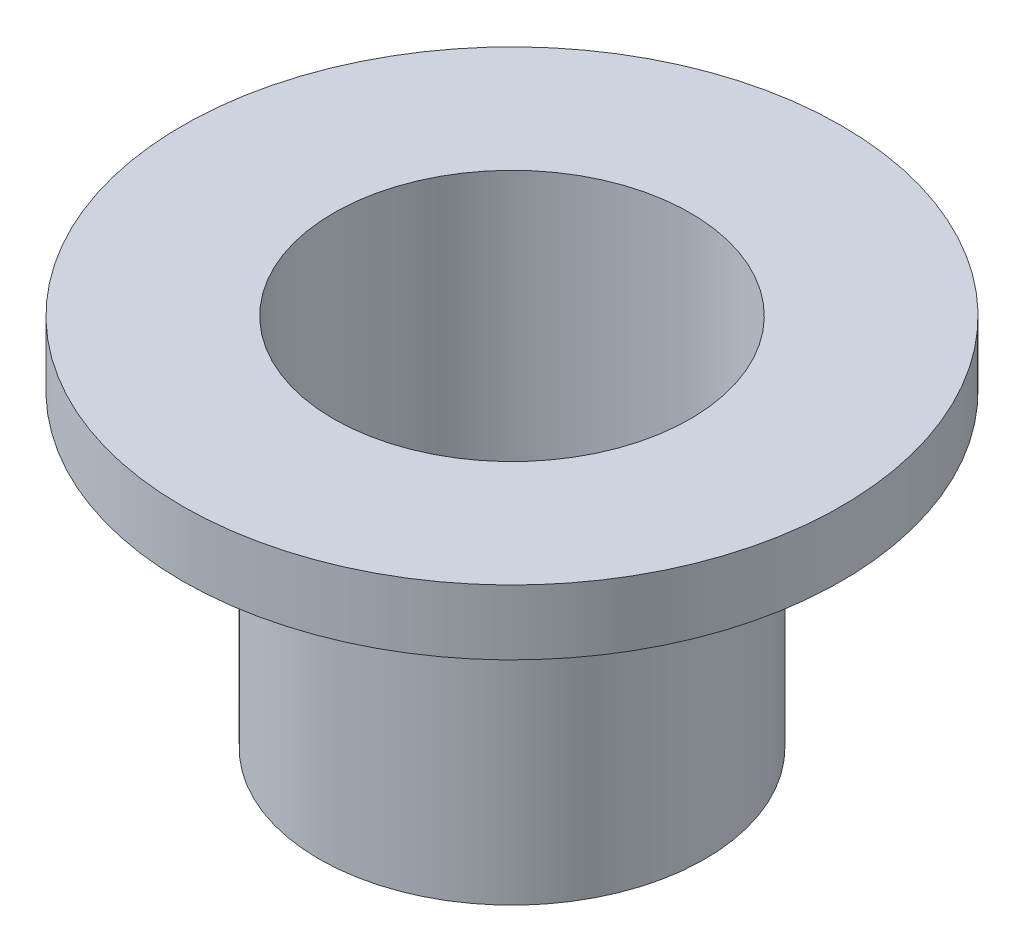
SolidWorks part; units mm, degrees
ref_plane "Front" through (0, 0, 0) normal (0, 0, 1) x (1, 0, 0)
ref_plane "Top" through (0, 0, 0) normal (0, 1, 0) x (1, 0, 0)
ref_plane "Right" through (0, 0, 0) normal (1, 0, 0) x (0, 0, -1)
sketch "Sketch1" plane through (0, 0, 0) normal (1, 0, 0) x (0, 0, -1)
  line L0 (0, 12.1047) -> (0, -8.1926) construction
  line L1 (2.75, 5.7625) -> (2.75, 0)
  line L2 (2.75, 0) -> (2.975, 0)
  line L3 (2.975, 0) -> (2.975, 4.7625)
  line L4 (2.975, 4.7625) -> (5.08, 4.7625)
  line L5 (5.08, 4.7625) -> (5.08, 5.7625)
  line L6 (5.08, 5.7625) -> (2.75, 5.7625)
  point P3 (2.8625, 0)
  dimension "D1" = 2.975
  dimension "D2" = 2.75
  dimension "D3" = 1
  dimension "D4" = 4.7625
  dimension "D5" = 5.08
revolve "Revolve1" add sketch "Sketch1" angle 360 about L0
